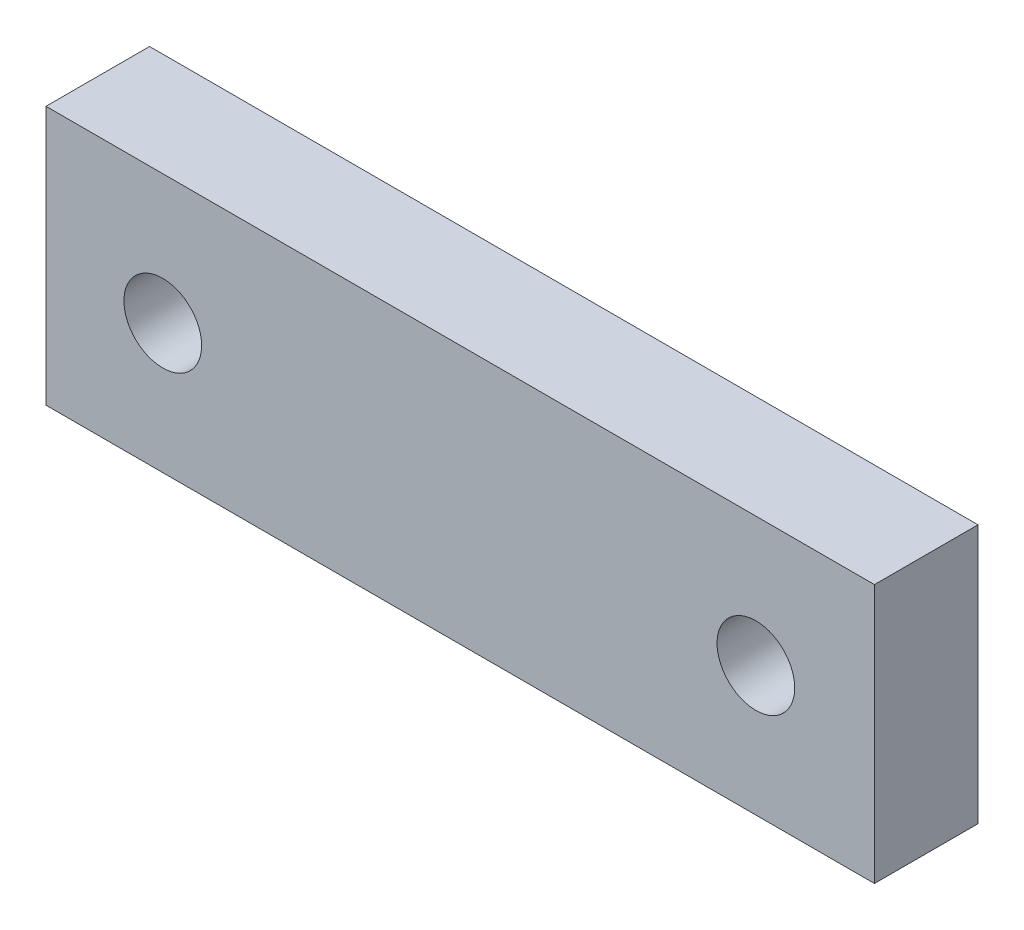
SolidWorks part; units mm, degrees
ref_plane "Plano frontal" through (0, 0, 0) normal (0, 0, 1) x (1, 0, 0)
ref_plane "Plano superior" through (0, 0, 0) normal (0, 1, 0) x (1, 0, 0)
ref_plane "Plano direito" through (0, 0, 0) normal (1, 0, 0) x (0, 0, -1)
sketch "Esboço1" plane through (0, 0, 0) normal (0, 0, 1) x (1, 0, 0)
  line L1 (0, 0) -> (32, 0)
  line L2 (0, 0) -> (0, -10)
  line L3 (0, -10) -> (32, -10)
  line L4 (32, 0) -> (32, -10)
  dimension "D1" = 32
  dimension "D2" = 10
extrude "Ressalto-extrusão1" add sketch "Esboço1" along normal blind 4
sketch "Esboço2" plane through (0, 0, 4) normal (0, 0, 1) x (1, 0, 0)
  line L0 (0, -5) -> (32, -5) construction
  line L1 (0, 0) -> (0, -10) construction
  line L2 (32, -10) -> (32, 0) construction
  line L3 (16, 0) -> (16, -10) construction
  line L4 (32, 0) -> (0, 0) construction
  line L5 (0, -10) -> (32, -10) construction
  circle A0 centre (4.51, -5) radius 1.5
  circle A1 centre (27.42, -5) radius 1.5
  dimension "D1" = 3
  dimension "D4" = 3
  dimension "D2" = 11.49
  dimension "D3" = 11.42
extrude "Corte-extrusão1" cut sketch "Esboço2" against normal blind 4
